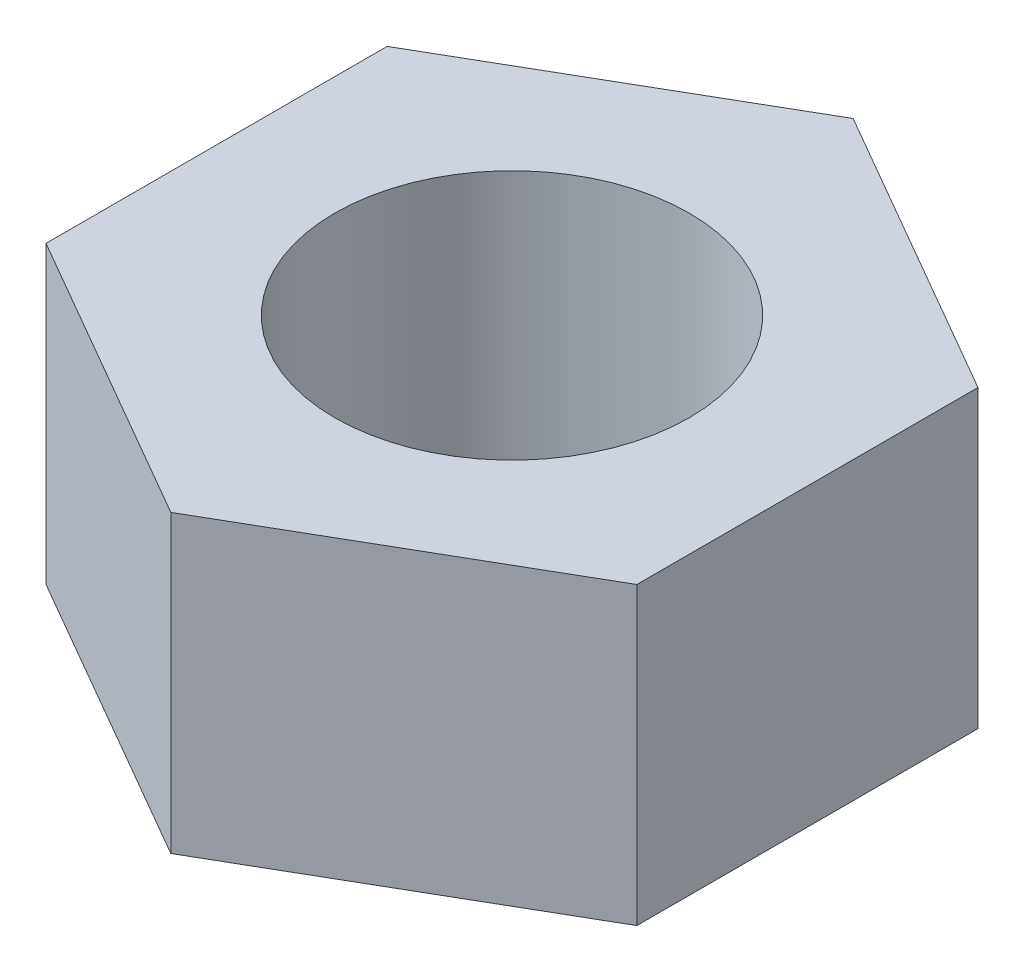
SolidWorks part; units mm, degrees
ref_plane "Plan de face" through (0, 0, 0) normal (0, 0, 1) x (1, 0, 0)
ref_plane "Plan de dessus" through (0, 0, 0) normal (0, 1, 0) x (1, 0, 0)
ref_plane "Plan de droite" through (0, 0, 0) normal (1, 0, 0) x (0, 0, -1)
sketch "Esquisse1" plane through (0, 0, 0) normal (0, 1, 0) x (1, 0, 0)
  line L0 (-5, 2.8868) -> (0, 5.7735)
  line L1 (-5, 2.8868) -> (5, 2.8868) construction
  line L2 (-5, 2.8868) -> (-5, -2.8868)
  line L3 (-5, -2.8868) -> (5, -2.8868) construction
  line L4 (5, 2.8868) -> (5, -2.8868)
  line L5 (-5, 2.8868) -> (5, -2.8868) construction
  line L6 (-5, -2.8868) -> (5, 2.8868) construction
  line L7 (0, 5.7735) -> (5, 2.8868)
  line L8 (-5, -2.8868) -> (0, -5.7735)
  line L9 (0, -5.7735) -> (5, -2.8868)
  circle A0 centre (0, 0) radius 3
  point P7 (-62.2995, 39.0923)
  dimension "D3" = 6
  dimension "D1" = 120
  dimension "D2" = 10
extrude "Boss.-Extru.1" add sketch "Esquisse1" along normal blind 5
